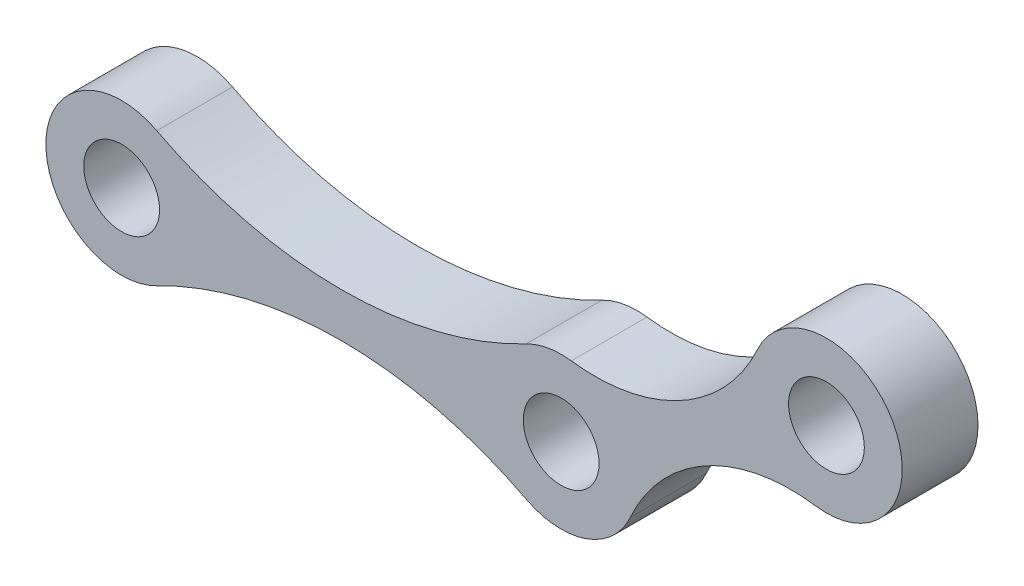
SolidWorks part; units mm, degrees
ref_plane "前基準面" through (0, 0, 0) normal (0, 0, 1) x (1, 0, 0)
ref_plane "上基準面" through (0, 0, 0) normal (0, 1, 0) x (1, 0, 0)
ref_plane "右基準面" through (0, 0, 0) normal (1, 0, 0) x (0, 0, -1)
sketch "草圖1" plane through (0, 0, 0) normal (0, 0, 1) x (1, 0, 0)
  line L0 (0, 0) -> (46.5043, 9.6747) construction
  line L1 (46.5043, 9.6747) -> (29, 0) construction
  line L2 (29, 0) -> (0, 0) construction
  line L3 (45.4859, 14.5699) -> (-1.0184, 4.8952)
  line L4 (0, -5) -> (29, -5)
  line L5 (31.4187, -4.3761) -> (48.923, 5.2986)
  circle A0 centre (46.5043, 9.6747) radius 2.5
  circle A1 centre (29, 0) radius 2.5
  circle A2 centre (0, 0) radius 2.5
  arc A3 (29, -5) -> (31.4187, -4.3761) centre (29, 0) ccw
  arc A4 (48.923, 5.2986) -> (45.4859, 14.5699) centre (46.5043, 9.6747) ccw
  arc A5 (-1.0184, 4.8952) -> (0, -5) centre (0, 0) ccw
  circle A6 centre (29, 0) radius 5 construction
  circle A7 centre (46.5043, 9.6747) radius 5 construction
  circle A8 centre (0, 0) radius 5 construction
  dimension "D4" = 5
  dimension "D1" = 47.5
  dimension "D2" = 20
  dimension "D3" = 29
  dimension "D5" = 2.5
extrude "填料-伸長1" add sketch "草圖1" along normal mid plane 5
sketch "草圖2" plane through (0, 0, 2.5) normal (0, 0, 1) x (1, 0, 0)
  arc A0 (29, -5) -> (31.4187, -4.3761) centre (29, 0) ccw construction
  arc A1 (-1.0184, 4.8952) -> (0, -5) centre (0, 0) ccw construction
  arc A2 (48.923, 5.2986) -> (45.4859, 14.5699) centre (46.5043, 9.6747) ccw construction
  arc A3 (45.7934, 4.7255) -> (41.9532, 11.7453) centre (46.5043, 9.6747) ccw
  arc A4 (26.7052, -4.4423) -> (33.5689, -2.031) centre (29, 0) ccw
  arc A5 (2.3171, 4.4307) -> (2.2948, -4.4423) centre (0, 0) ccw
  arc A6 (41.9532, 11.7453) -> (29.6679, 4.9552) centre (31.24, 16.6197) cw
  arc A7 (26.6829, 4.4307) -> (2.3171, 4.4307) centre (14.5, 27.7268) cw
  arc A8 (45.7934, 4.7255) -> (33.5689, -2.031) centre (44.1474, -6.7336) ccw
  arc A9 (26.7052, -4.4423) -> (2.2948, -4.4423) centre (14.5, -28.0695) ccw
  arc A10 (29.6679, 4.9552) -> (26.6829, 4.4307) centre (29, 0) ccw
  point P1 (26.7052, 4.4307)
  point P3 (30.2489, -4.8415)
extrude "除料-伸長1" cut sketch "草圖2" against normal blind 5 flip side to cut
